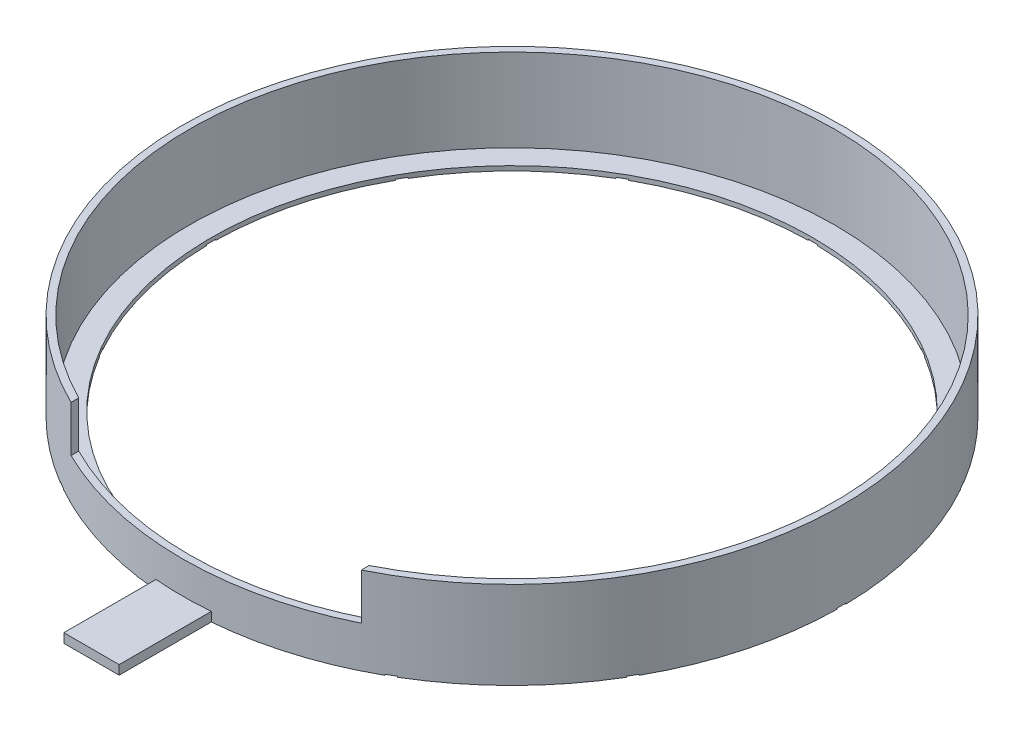
SolidWorks part; units mm, degrees
ref_plane "前视基准面" through (0, 0, 0) normal (0, 0, 1) x (1, 0, 0)
ref_plane "上视基准面" through (0, 0, 0) normal (0, 1, 0) x (1, 0, 0)
ref_plane "右视基准面" through (0, 0, 0) normal (1, 0, 0) x (0, 0, -1)
sketch "草图1" plane through (0, 0, 0) normal (0, 1, 0) x (1, 0, 0)
  circle A0 centre (0, 0) radius 71.5
  circle A1 centre (0, 0) radius 70
  dimension "D1" = 143
  dimension "D2" = 140
extrude "凸台-拉伸1" add sketch "草图1" along normal blind 19
sketch "草图2" plane through (0, 0, 0) normal (0, -1, 0) x (1, 0, 0)
  circle A0 centre (0, 0) radius 71.5
  circle A1 centre (0, 0) radius 65.25
  circle A2 centre (0, 0) radius 71.5 construction
  dimension "D1" = 130.5
extrude "凸台-拉伸2" add sketch "草图2" against normal blind 1
sketch "草图4" plane through (0, 19, 0) normal (0, 1, 0) x (1, 0, 0)
  line L0 (0, 0) -> (0, -83.4751) construction
  line L1 (-31.5, 0) -> (-31.5, -83.4751)
  line L2 (-31.5, -83.4751) -> (0, -83.4751)
  line L3 (0, -83.4751) -> (31.5, -83.4751)
  line L4 (31.5, -83.4751) -> (31.5, 0)
  line L5 (31.5, 0) -> (-31.5, 0)
  dimension "D1" = 63
extrude "切除-拉伸1" cut sketch "草图4" against normal blind 10
sketch "草图5" plane through (0, 0, 0) normal (0, -1, 0) x (1, 0, 0)
  line L0 (0, 0) -> (0, 132.5992) construction
  line L2 (6, 71.2478) -> (6, 91.2478)
  line L3 (6, 91.2478) -> (-6, 91.2478)
  line L4 (-6, 71.2478) -> (-6, 91.2478)
  circle A1 centre (0, 0) radius 71.5 construction
  arc A2 (6, 71.2478) -> (-6, 71.2478) centre (0, 0) ccw
  point P0 (0, 80.4258)
  dimension "D1" = 12
  dimension "D2" = 20
extrude "凸台-拉伸4" add sketch "草图5" against normal blind 2
sketch "草图6" plane through (0, 0, 0) normal (0, -1, 0) x (1, 0, 0)
  line L0 (0, 0) -> (0, -103.1675) construction
  line L2 (-1, -71.493) -> (-1, -65.2423)
  line L3 (-1, -65.2423) -> (1, -65.2423)
  line L4 (1, -71.493) -> (1, -65.2423)
  line L5 (-36.6125, -61.4148) -> (-33.4872, -56.0015)
  line L6 (-34.8805, -62.4148) -> (-31.7551, -57.0015)
  line L7 (-62.4148, -34.8805) -> (-57.0015, -31.7551)
  line L8 (-61.4148, -36.6125) -> (-56.0015, -33.4872)
  line L9 (-71.493, 1) -> (-65.2423, 1)
  line L10 (-71.493, -1) -> (-65.2423, -1)
  line L11 (-61.4148, 36.6125) -> (-56.0015, 33.4872)
  line L12 (-62.4148, 34.8805) -> (-57.0015, 31.7551)
  line L13 (-34.8805, 62.4148) -> (-31.7551, 57.0015)
  line L14 (-36.6125, 61.4148) -> (-33.4872, 56.0015)
  line L15 (1, 71.493) -> (1, 65.2423)
  line L16 (-1, 71.493) -> (-1, 65.2423)
  line L17 (36.6125, 61.4148) -> (33.4872, 56.0015)
  line L18 (34.8805, 62.4148) -> (31.7551, 57.0015)
  line L19 (62.4148, 34.8805) -> (57.0015, 31.7551)
  line L20 (61.4148, 36.6125) -> (56.0015, 33.4872)
  line L21 (71.493, -1) -> (65.2423, -1)
  line L22 (71.493, 1) -> (65.2423, 1)
  line L23 (61.4148, -36.6125) -> (56.0015, -33.4872)
  line L24 (62.4148, -34.8805) -> (57.0015, -31.7551)
  line L25 (34.8805, -62.4148) -> (31.7551, -57.0015)
  line L26 (36.6125, -61.4148) -> (33.4872, -56.0015)
  circle A0 centre (0, 0) radius 65.25 construction
  arc A1 (-6, 71.2478) -> (6, 71.2478) centre (0, 0) ccw construction
  arc A2 (-34.8805, 62.4148) -> (-36.6125, 61.4148) centre (0, 0) ccw
  arc A3 (-31.7551, 57.0015) -> (-33.4872, 56.0015) centre (0, 0) ccw
  arc A4 (1, 71.493) -> (-1, 71.493) centre (0, 0) ccw
  arc A5 (1, 65.2423) -> (-1, 65.2423) centre (0, 0) ccw
  arc A6 (33.4872, 56.0015) -> (31.7551, 57.0015) centre (0, 0) ccw
  arc A7 (36.6125, 61.4148) -> (34.8805, 62.4148) centre (0, 0) ccw
  arc A8 (57.0015, 31.7551) -> (56.0015, 33.4872) centre (0, 0) ccw
  arc A9 (62.4148, 34.8805) -> (61.4148, 36.6125) centre (0, 0) ccw
  arc A10 (65.2423, -1) -> (65.2423, 1) centre (0, 0) ccw
  arc A11 (71.493, -1) -> (71.493, 1) centre (0, 0) ccw
  arc A12 (56.0015, -33.4872) -> (57.0015, -31.7551) centre (0, 0) ccw
  arc A13 (61.4148, -36.6125) -> (62.4148, -34.8805) centre (0, 0) ccw
  arc A14 (31.7551, -57.0015) -> (33.4872, -56.0015) centre (0, 0) ccw
  arc A15 (34.8805, -62.4148) -> (36.6125, -61.4148) centre (0, 0) ccw
  arc A16 (-56.0015, 33.4872) -> (-57.0015, 31.7551) centre (0, 0) ccw
  arc A17 (-61.4148, 36.6125) -> (-62.4148, 34.8805) centre (0, 0) ccw
  arc A18 (-71.493, 1) -> (-71.493, -1) centre (0, 0) ccw
  arc A19 (-65.2423, 1) -> (-65.2423, -1) centre (0, 0) ccw
  arc A20 (-57.0015, -31.7551) -> (-56.0015, -33.4872) centre (0, 0) ccw
  arc A21 (-62.4148, -34.8805) -> (-61.4148, -36.6125) centre (0, 0) ccw
  arc A22 (-36.6125, -61.4148) -> (-34.8805, -62.4148) centre (0, 0) ccw
  arc A23 (-33.4872, -56.0015) -> (-31.7551, -57.0015) centre (0, 0) ccw
  arc A24 (-1, -65.2423) -> (1, -65.2423) centre (0, 0) ccw
  arc A25 (-1, -71.493) -> (1, -71.493) centre (0, 0) ccw
  point P0 (0, -70.7224)
  point P60 (0, 0)
  arc M7 (-6, 71.2478) -> (6, 71.2478) centre (0, 0) ccw
  circle M11 centre (0, 0) radius 65.25
  dimension "D1" = 2
  dimension "D2" = 12
extrude "切除-拉伸2" cut sketch "草图6" against normal blind 0.2 contours L0 A2 L4 M11 | L0 A3 L2 M7 | L26 L25 M7 M11 | L24 L23 M7 M11 | L22 L21 M7 M11 | L20 L19 M7 M11 | L18 L17 M7 M11 | L14 L13 M7 M11 | L12 L11 M7 M11 | L10 L9 M7 M11 | L8 L7 M7 M11 | L6 L5 M7 M11 | L16 A5 L15 A4
